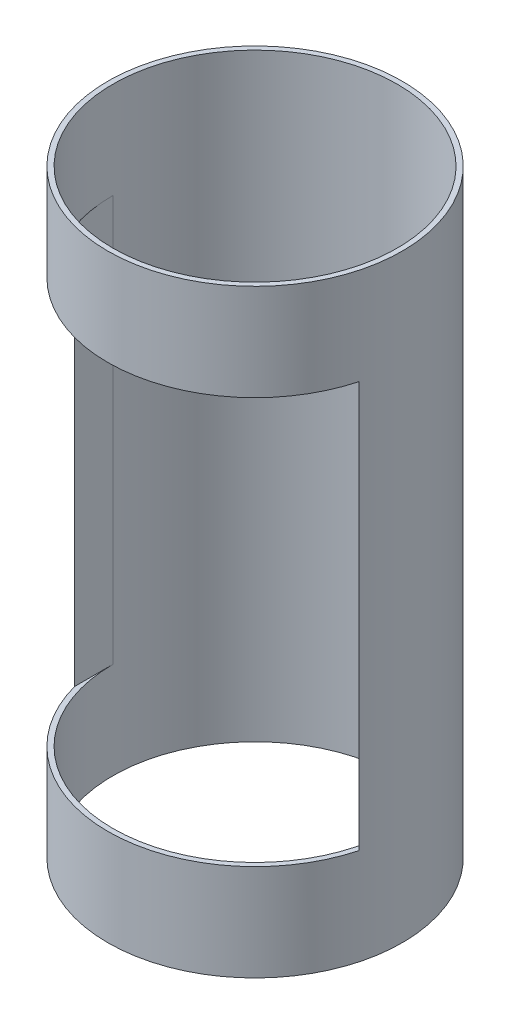
SolidWorks part; units mm, degrees
ref_plane "Front Plane" through (0, 0, 0) normal (0, 0, 1) x (1, 0, 0)
ref_plane "Top Plane" through (0, 0, 0) normal (0, 1, 0) x (1, 0, 0)
ref_plane "Right Plane" through (0, 0, 0) normal (1, 0, 0) x (0, 0, -1)
sketch "Sketch1" plane through (0, 0, 0) normal (0, 1, 0) x (1, 0, 0)
  circle A0 centre (0, 0) radius 88.9
  circle A1 centre (0, 0) radius 92.075
  dimension "D1" = 177.8
  dimension "D2" = 184.15
extrude "Boss-Extrude1" add sketch "Sketch1" along normal blind 374.65
sketch "Sketch2" plane through (0, 0, 0) normal (0, 0, 1) x (1, 0, 0)
  line L0 (0, 0) -> (0, 374.65) construction
  line L1 (88.9, 374.65) -> (-88.9, 374.65) construction
  line L2 (-92.075, 187.325) -> (92.075, 187.325) construction
  line L3 (-92.075, 374.65) -> (-92.075, 0) construction
  line L4 (92.075, 0) -> (92.075, 374.65) construction
  line L6 (-88.9, 60.325) -> (88.9, 60.325)
  line L7 (-88.9, 60.325) -> (-88.9, 314.325)
  line L8 (-88.9, 314.325) -> (88.9, 314.325)
  line L9 (88.9, 60.325) -> (88.9, 314.325)
  line L10 (-88.9, 60.325) -> (88.9, 314.325) construction
  line L11 (-88.9, 314.325) -> (88.9, 60.325) construction
  point P11 (0, 187.325)
  dimension "D1" = 177.8
  dimension "D2" = 254
extrude "Cut-Extrude1" cut sketch "Sketch2" along normal through all
